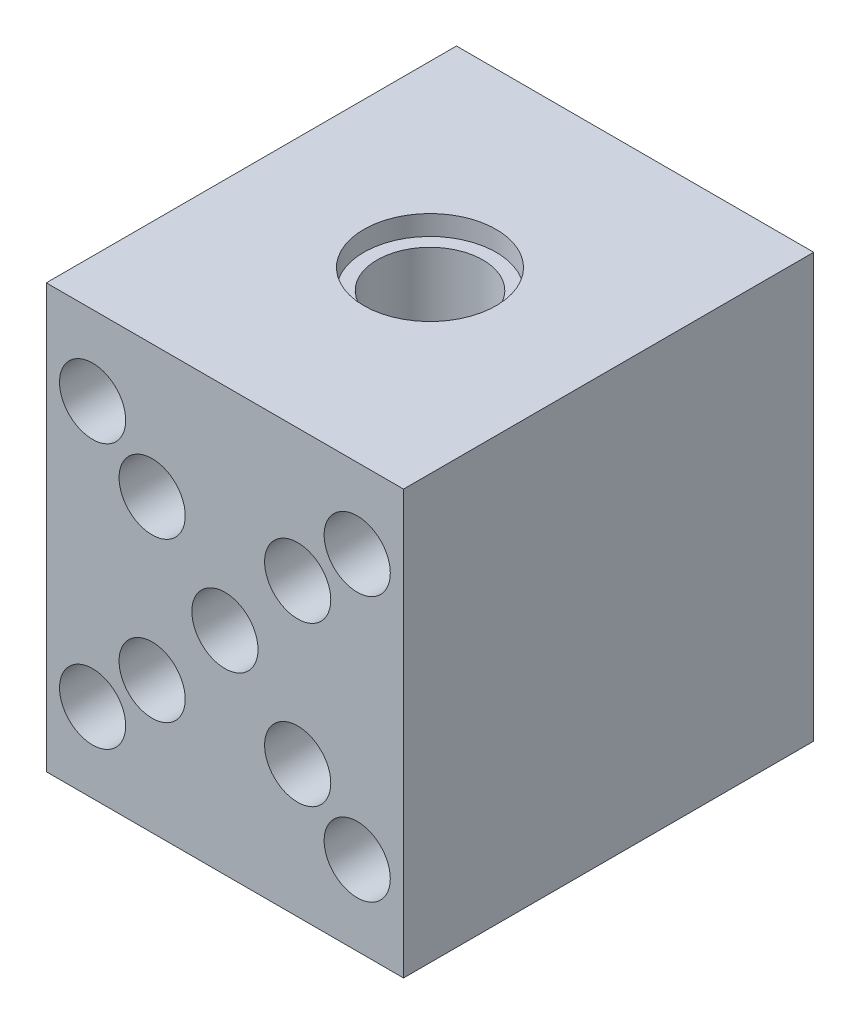
SolidWorks part; units mm, degrees
ref_plane "Piano frontale" through (0, 0, 0) normal (0, 0, 1) x (1, 0, 0)
ref_plane "Piano superiore" through (0, 0, 0) normal (0, 1, 0) x (1, 0, 0)
ref_plane "Piano destro" through (0, 0, 0) normal (1, 0, 0) x (0, 0, -1)
sketch "Schizzo1" plane through (0, 0, 0) normal (0, 0, 1) x (1, 0, 0)
  line L1 (-13.5, 16) -> (13.5, 16)
  line L2 (-13.5, 16) -> (-13.5, -16)
  line L3 (-13.5, -16) -> (13.5, -16)
  line L4 (13.5, 16) -> (13.5, -16)
  line L5 (-13.5, 16) -> (13.5, -16) construction
  line L6 (-13.5, -16) -> (13.5, 16) construction
  point P0 (0, 0)
  dimension "D1" = 27
  dimension "D2" = 32
extrude "Estrusione-Estrusione1" add sketch "Schizzo1" along normal blind 31
sketch "Schizzo2" plane through (0, 0, 0) normal (0, 0, -1) x (-1, 0, 0)
  line L1 (-10, 10) -> (10, 10) construction
  line L2 (-10, 10) -> (-10, -10) construction
  line L3 (-10, -10) -> (10, -10) construction
  line L4 (10, 10) -> (10, -10) construction
  line L5 (-10, 10) -> (10, -10) construction
  line L6 (-10, -10) -> (10, 10) construction
  circle A0 centre (-10, 10) radius 1.5
  circle A1 centre (10, 10) radius 1.5
  circle A2 centre (10, -10) radius 1.5
  circle A3 centre (-10, -10) radius 1.5
  point P0 (0, 0)
  dimension "D3" = 3
  dimension "D1" = 20
  dimension "D2" = 20
extrude "Taglio-Estrusione1" cut sketch "Schizzo2" against normal through all
sketch "Schizzo3" plane through (0, 16, 0) normal (0, 1, 0) x (1, 0, 0)
  line L1 (-13.5, 0) -> (13.5, -31) construction
  line L2 (13.5, 0) -> (-13.5, -31) construction
  circle A0 centre (0, -15.5) radius 4
  point P11 (0, -15.5)
  dimension "D1" = 8
extrude "Taglio-Estrusione2" cut sketch "Schizzo3" against normal through all
sketch "Schizzo4" plane through (0, 16, 0) normal (0, 1, 0) x (1, 0, 0)
  circle A0 centre (0, -15.5) radius 5
  circle A1 centre (0, -15.5) radius 4 construction
  dimension "D1" = 10
extrude "Taglio-Estrusione5" cut sketch "Schizzo4" against normal blind 1.5
sketch "Schizzo5" plane through (0, -16, 0) normal (0, -1, 0) x (1, 0, 0)
  circle A0 centre (0, 15.5) radius 5
  circle A1 centre (0, 15.5) radius 4 construction
  dimension "D1" = 10
extrude "Taglio-Estrusione6" cut sketch "Schizzo5" against normal blind 1.5
sketch "Schizzo6" plane through (0, 0, 31) normal (0, 0, 1) x (1, 0, 0)
  line L1 (-10, 10) -> (10, 10) construction
  line L2 (-10, 10) -> (-10, -10) construction
  line L3 (-10, -10) -> (10, -10) construction
  line L4 (10, 10) -> (10, -10) construction
  line L5 (-10, 10) -> (10, -10) construction
  line L6 (-10, -10) -> (10, 10) construction
  circle A0 centre (-10, 10) radius 2.5
  circle A1 centre (10, 10) radius 2.5
  circle A2 centre (10, -10) radius 2.5
  circle A3 centre (-10, -10) radius 2.5
  point P0 (0, 0)
  dimension "D1" = 5
extrude "Taglio-Estrusione7" cut sketch "Schizzo6" against normal blind 15
sketch "Schizzo7" plane through (0, 0, 31) normal (0, 0, 1) x (1, 0, 0)
  line L0 (-13.5, 16) -> (-13.5, -16) construction
  line L1 (-5.5, 6) -> (5.5, 6) construction
  line L2 (-5.5, 6) -> (-5.5, -6) construction
  line L3 (-5.5, -6) -> (5.5, -6) construction
  line L4 (5.5, 6) -> (5.5, -6) construction
  line L5 (-5.5, 6) -> (5.5, -6) construction
  line L6 (-5.5, -6) -> (5.5, 6) construction
  line L9 (-13.5, -16) -> (13.5, -16) construction
  circle A0 centre (-5.5, 6) radius 2.5
  circle A1 centre (5.5, 6) radius 2.5
  circle A2 centre (0, 0) radius 2.5
  circle A3 centre (5.5, -6) radius 2.5
  circle A4 centre (-5.5, -6) radius 2.5
  point P0 (0, 0)
  dimension "D3" = 5
  dimension "D1" = 8
  dimension "D2" = 10
extrude "Taglio-Estrusione8" cut sketch "Schizzo7" against normal blind 10
